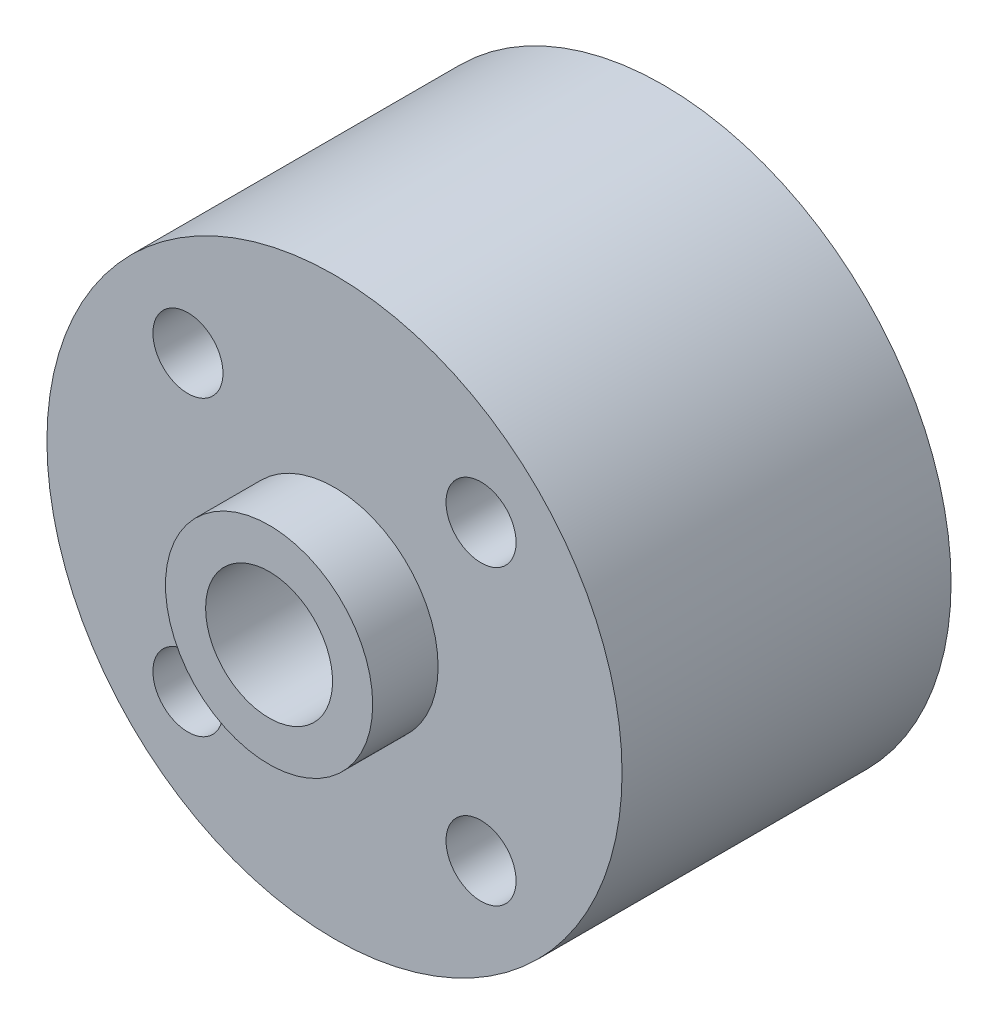
SolidWorks part; units mm, degrees
material "2024 Alloy"
ref_plane "Front Plane" through (0, 0, 0) normal (0, 0, 1) x (1, 0, 0)
ref_plane "Top Plane" through (0, 0, 0) normal (0, 1, 0) x (1, 0, 0)
ref_plane "Right Plane" through (0, 0, 0) normal (1, 0, 0) x (0, 0, -1)
sketch "Sketch1" plane through (0, 0, 0) normal (0, 1, 0) x (1, 0, 0)
  line L0 (11.1, 6.35) -> (0, 6.35)
  line L1 (0, 6.35) -> (0, -6.35)
  line L2 (0, -6.35) -> (11.1, -6.35)
  line L3 (11.1, -6.35) -> (11.1, 6.35)
  line L4 (0, 6.35) -> (0, -6.35) construction
revolve "Revolve1" add sketch "Sketch1" angle 360 about L4
sketch "Sketch2" plane through (0, 0, -6.35) normal (0, 0, -1) x (-1, 0, 0)
  circle A0 centre (0, 0) radius 4
extrude "Boss-Extrude1" add sketch "Sketch2" along normal blind 2.525
sketch "Sketch3" plane through (0, 0, 6.35) normal (0, 0, 1) x (1, 0, 0)
  circle A0 centre (0, 0) radius 4
extrude "Boss-Extrude2" add sketch "Sketch3" along normal blind 2.525
hole_wizard "M2.5 Clearance Hole1" positions "Sketch5" profile "Sketch4" hole size "M2.5" standard "ANSI Metric"
sketch "Sketch5" plane through (0, 0, 6.35) normal (0, 0, 1) x (1, 0, 0)
  point P0 (5.6569, 5.6569)
  point P1 (-5.6569, 5.6569)
  point P2 (-5.6569, -5.6569)
  point P3 (5.6569, -5.6569)
sketch "Sketch4" plane through (5.6569, 5.6569, 6.35) normal (1, 0, 0) x (0, -1, 0)
  line L0 (0, 0) -> (0, 15.225)
  line L1 (0, 15.225) -> (1.3525, 15.225)
  line L2 (1.3525, 15.225) -> (1.3525, 0)
  line L5 (1.3525, 0) -> (0, 0)
  line L11 (0, -6.35) -> (0, 107.95) construction
  dimension "Thru Hole Dia." = 2.705
  dimension "Thru Hole Depth" = 15.225
hole_wizard "Ø4.9 (4.9) Diameter Hole1" positions "Sketch7" profile "Sketch6" hole size "Ø4.9" standard "ANSI Metric"
sketch "Sketch7" plane through (0, 0, -8.875) normal (0, 0, -1) x (-1, 0, 0)
  point P0 (0, 0)
sketch "Sketch6" plane through (0, 0, -8.875) normal (1, 0, 0) x (0, 1, 0)
  line L0 (0, 0) -> (0, 17.75)
  line L1 (0, 17.75) -> (2.45, 17.75)
  line L2 (2.45, 17.75) -> (2.45, 0)
  line L5 (2.45, 0) -> (0, 0)
  line L11 (0, -6.35) -> (0, 107.95) construction
  dimension "Thru Hole Dia." = 4.9
  dimension "Thru Hole Depth" = 17.75
